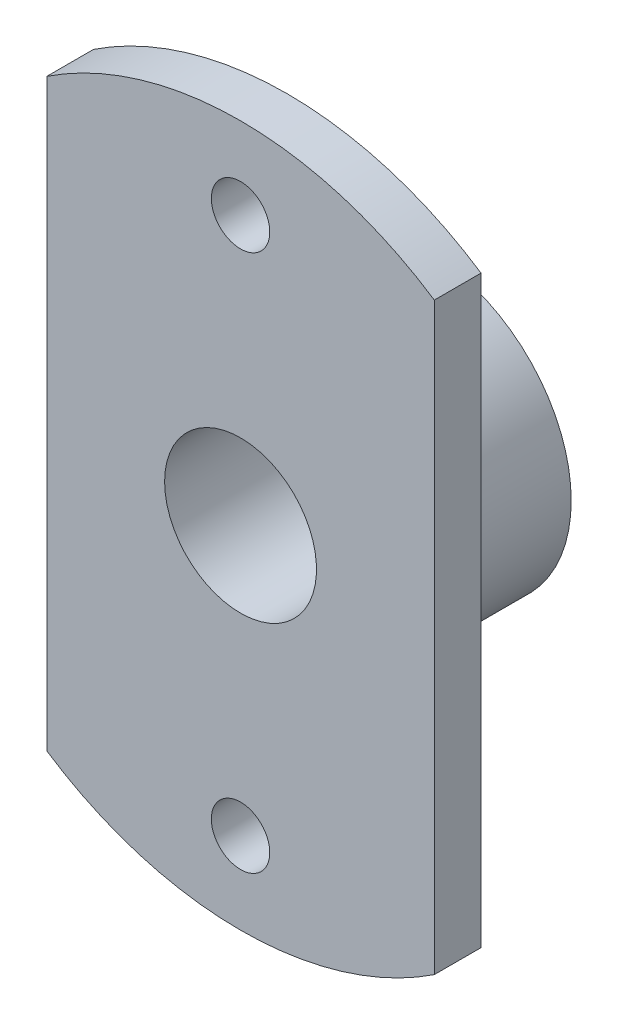
SolidWorks part; units mm, degrees
ref_plane "Front Plane" through (0, 0, 0) normal (1, 0, 0) x (0, 1, 0)
ref_plane "Top Plane" through (0, 0, 0) normal (0, 0, 1) x (0, 1, 0)
ref_plane "Right Plane" through (0, 0, 0) normal (0, 1, 0) x (-1, 0, 0)
sketch "Sketch1" plane through (0, 0, 0) normal (0, 0, 1) x (0, 1, 0)
  circle A0 centre (0, 0) radius 12.3
  dimension "D1" = 24.6
extrude "Boss-Extrude1" add sketch "Sketch1" along normal blind 12
sketch "Sketch2" plane through (0, 0, 12) normal (0, 0, 1) x (1, 0, 0)
  circle A0 centre (0, 0) radius 30
  dimension "D1" = 60
extrude "Boss-Extrude2" add sketch "Sketch2" along normal blind 4
sketch "Sketch3" plane through (0, 0, 12) normal (0, 0, -1) x (1, 0, 0)
  circle A0 centre (0, 23) radius 2.5
  circle A1 centre (0, -23) radius 2.5
  dimension "D3" = 5
  dimension "D1" = 23
  dimension "D2" = 23
extrude "Cut-Extrude1" cut sketch "Sketch3" against normal through all
sketch "Sketch4" plane through (0, 0, 0) normal (0, 0, -1) x (1, 0, 0)
  circle A0 centre (0, 0) radius 6.5
  dimension "D1" = 13
extrude "Cut-Extrude2" cut sketch "Sketch4" against normal through all
sketch "Sketch5" plane through (0, 0, 12) normal (0, 0, -1) x (1, 0, 0)
  line L1 (-16.5831, -25) -> (16.5831, -25) construction
  line L2 (-16.5831, -25) -> (-16.5831, 25)
  line L3 (-16.5831, 25) -> (16.5831, 25) construction
  line L4 (16.5831, -25) -> (16.5831, 25)
  line L5 (-16.5831, -25) -> (16.5831, 25) construction
  line L6 (-16.5831, 25) -> (16.5831, -25) construction
  circle A0 centre (0, 0) radius 30 construction
  arc A1 (-16.5831, 25) -> (-16.5831, -25) centre (0, 0) ccw
  arc A2 (16.5831, 25) -> (-16.5831, 25) centre (0, 0) ccw construction
  arc A3 (-16.5831, -25) -> (16.5831, -25) centre (0, 0) ccw construction
  arc A4 (16.5831, -25) -> (16.5831, 25) centre (0, 0) ccw
  point P0 (0, 0)
  dimension "D1" = 50
extrude "Cut-Extrude3" cut sketch "Sketch5" against normal through all
equation "\"D2@Sketch3\"=\"D1@Sketch3\""
